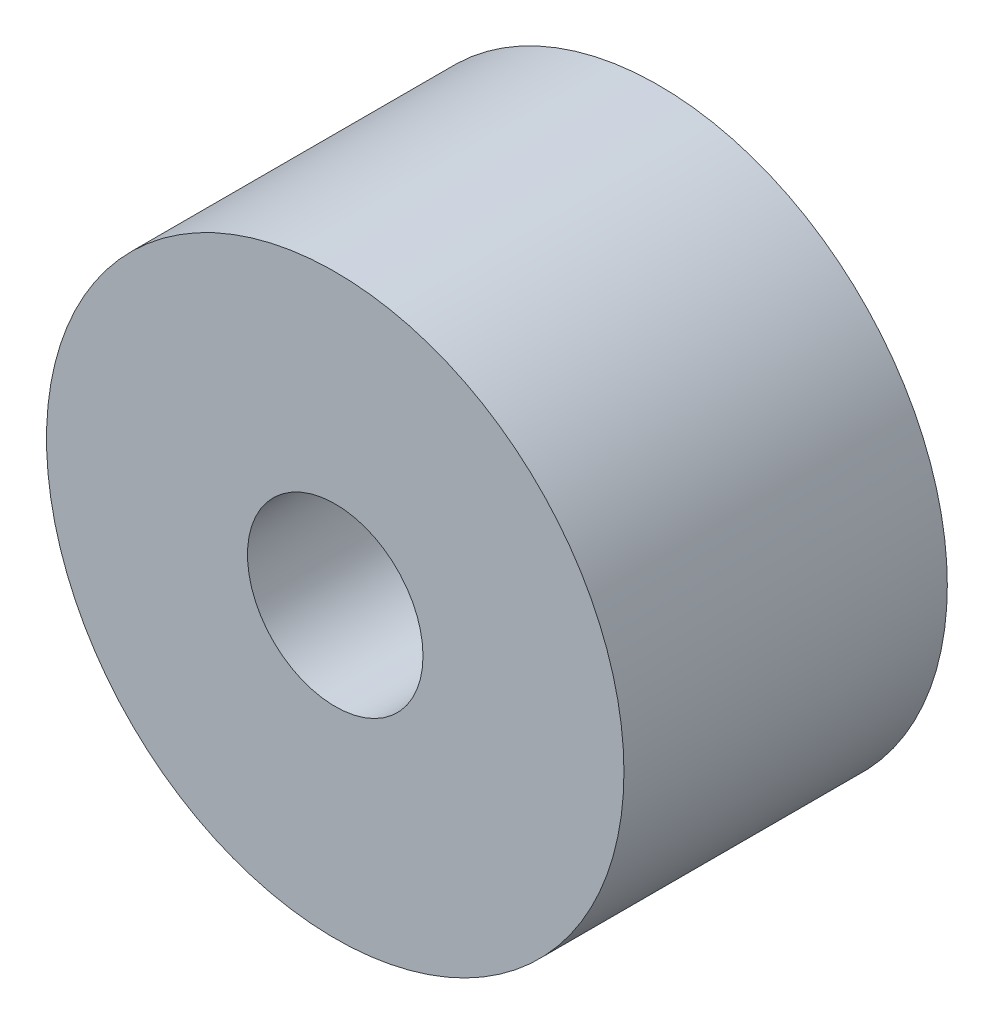
SolidWorks part; units mm, degrees
ref_plane "Front Plane" through (0, 0, 0) normal (0, 0, 1) x (1, 0, 0)
ref_plane "Top Plane" through (0, 0, 0) normal (0, 1, 0) x (1, 0, 0)
ref_plane "Right Plane" through (0, 0, 0) normal (1, 0, 0) x (0, 0, -1)
sketch "Sketch1" plane through (0, 0, 0) normal (0, 0, 1) x (1, 0, 0)
  circle A0 centre (0, 0) radius 62.5
  circle A1 centre (0, 0) radius 19
extrude "Boss-Extrude1" add sketch "Sketch1" along normal blind 70
